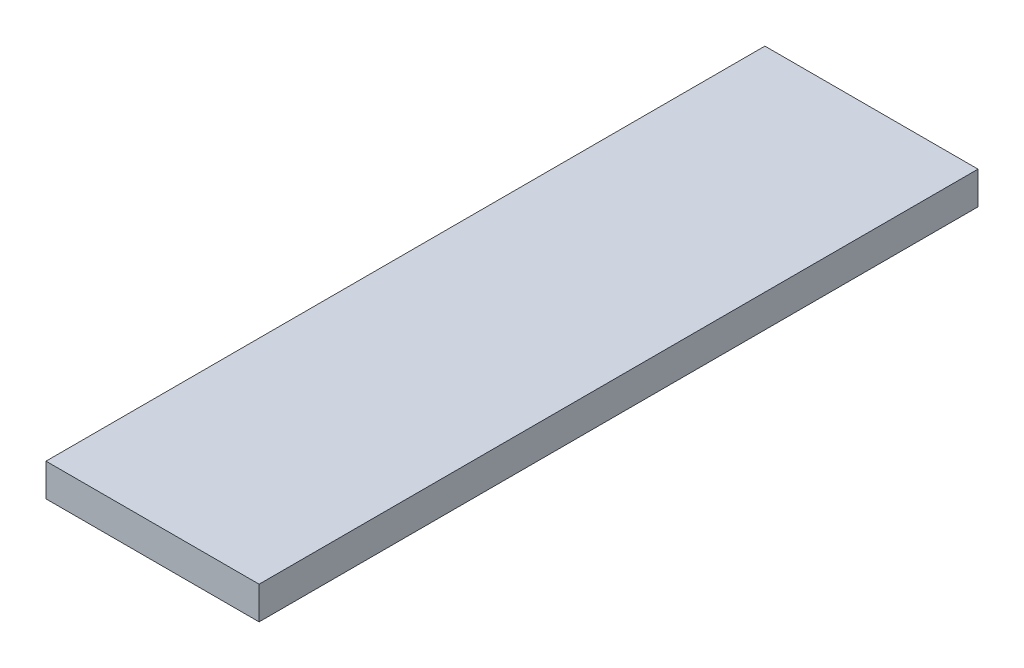
SolidWorks part; units mm, degrees
ref_plane "Front Plane" through (0, 0, 0) normal (0, 0, 1) x (1, 0, 0)
ref_plane "Top Plane" through (0, 0, 0) normal (0, 1, 0) x (1, 0, 0)
ref_plane "Right Plane" through (0, 0, 0) normal (1, 0, 0) x (0, 0, -1)
sketch "Sketch1" plane through (0, 0, 0) normal (0, 1, 0) x (1, 0, 0)
  line L1 (-20.7058, 69.85) -> (20.7058, 69.85)
  line L2 (-20.7058, 69.85) -> (-20.7058, -69.85)
  line L3 (-20.7058, -69.85) -> (20.7058, -69.85)
  line L4 (20.7058, 69.85) -> (20.7058, -69.85)
  line L5 (-20.7058, 69.85) -> (20.7058, -69.85) construction
  line L6 (-20.7058, -69.85) -> (20.7058, 69.85) construction
  point P0 (0, 0)
  point P6 (22.6828, 69.85)
  point P7 (20.7058, 69.85)
  dimension "D1" = 139.7
extrude "Boss-Extrude1" add sketch "Sketch1" against normal blind 6.35
